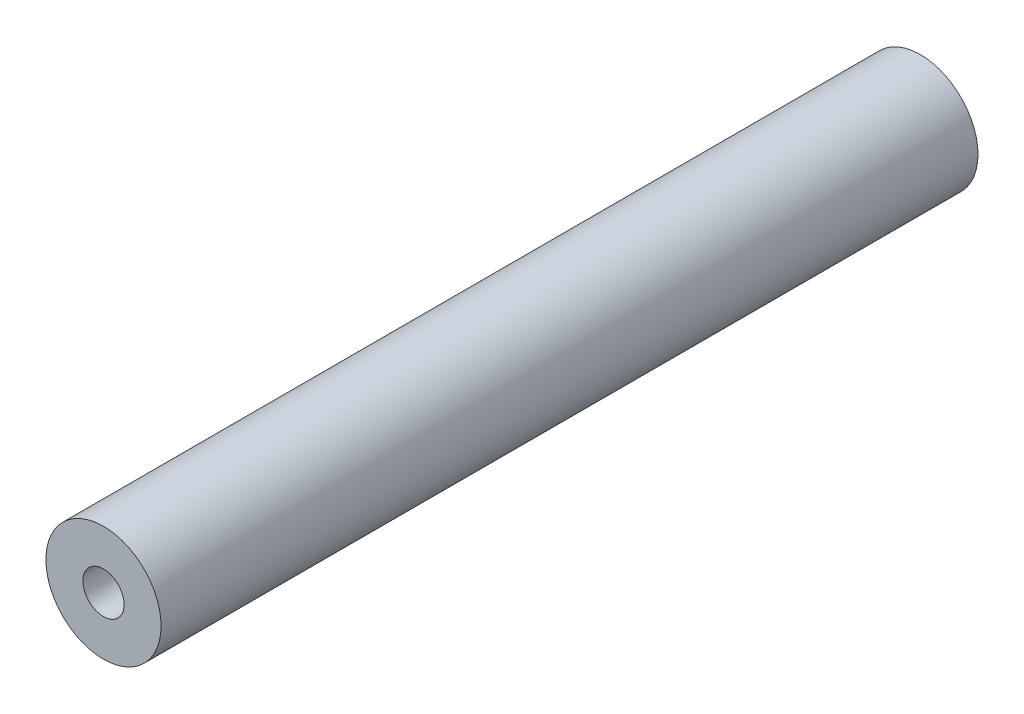
SolidWorks part; units mm, degrees
ref_plane "Front Plane" through (0, 0, 0) normal (0, 0, 1) x (1, 0, 0)
ref_plane "Top Plane" through (0, 0, 0) normal (0, 1, 0) x (1, 0, 0)
ref_plane "Right Plane" through (0, 0, 0) normal (1, 0, 0) x (0, 0, -1)
sketch "Sketch1" plane through (0, 0, 0) normal (0, 0, 1) x (1, 0, 0)
  circle A0 centre (0, 0) radius 4.826
  circle A1 centre (0, 0) radius 1.7272
  dimension "D1" = 3.4544
  dimension "D2" = 9.652
extrude "Boss-Extrude1" add sketch "Sketch1" along normal blind 68.453
